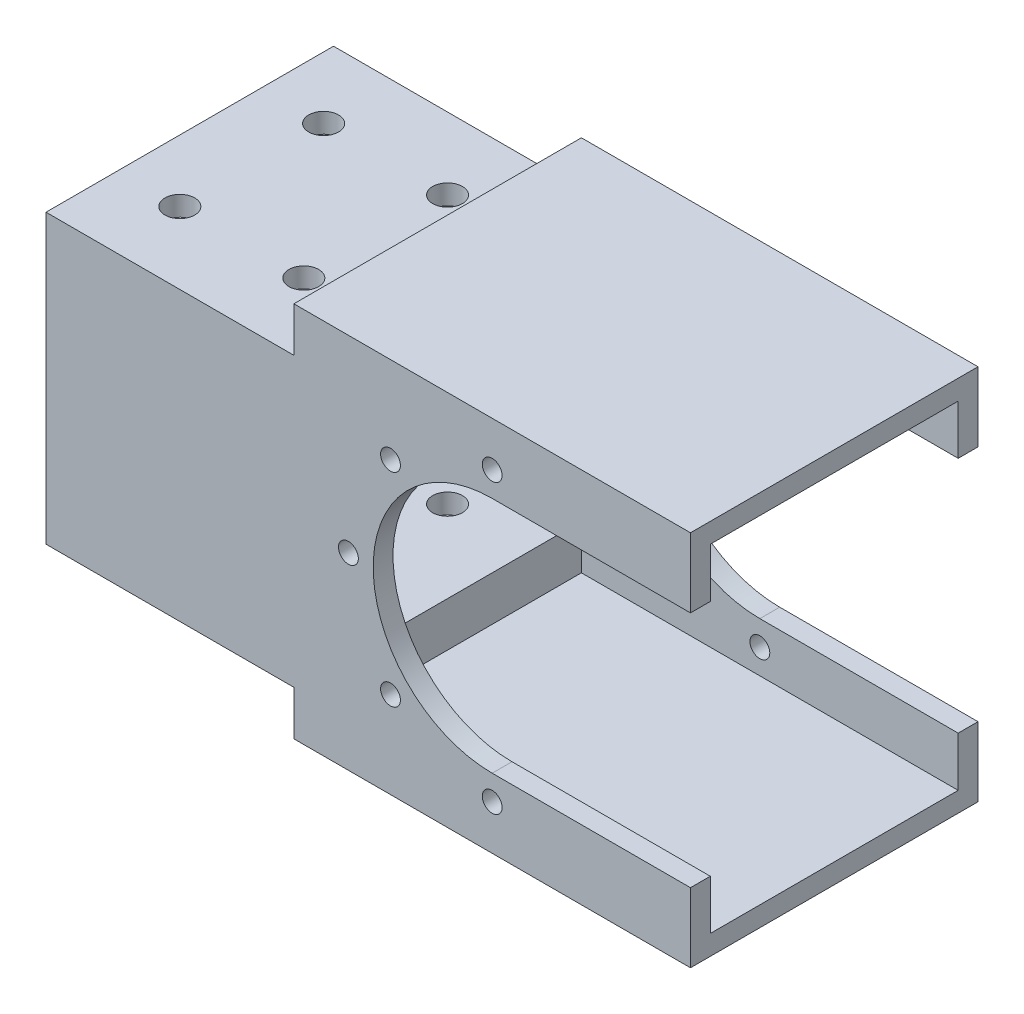
SolidWorks part; units mm, degrees
material "Plain Carbon Steel"
ref_plane "Front Plane" through (0, 0, 0) normal (0, 0, 1) x (1, 0, 0)
ref_plane "Top Plane" through (0, 0, 0) normal (0, 1, 0) x (1, 0, 0)
ref_plane "Right Plane" through (0, 0, 0) normal (1, 0, 0) x (0, 0, -1)
sketch "Sketch1" plane through (0, 0, 0) normal (0, 0, 1) x (1, 0, 0)
  line L0 (25, -62.3909) -> (25, -29) construction
  line L1 (-25, -29) -> (25, -29)
  line L2 (-25, -29) -> (-25, 29)
  line L3 (-25, 29) -> (25, 29)
  line L5 (0, 29) -> (0, -29) construction
  line L6 (-25, 0) -> (50, 0) construction
  line L7 (25, 38) -> (25, 29)
  line L8 (25, 38) -> (105, 38)
  line L9 (25, -38) -> (105, -38)
  line L10 (105, 38) -> (105, -38)
  line L11 (25, 29) -> (25, 60.3909) construction
  line L12 (25, -29) -> (25, -38)
  point P0 (0, 0)
  point P4 (105, 0)
  point P7 (50, 0)
  dimension "D1" = 50
  dimension "D2" = 58
  dimension "D3" = 76
  dimension "D4" = 80
extrude "Boss-Extrude1" add sketch "Sketch1" along normal blind 58
shell "Shell1" thickness 4
sketch "Sketch2" plane through (0, 0, 0) normal (0, 0, -1) x (-1, 0, 0)
  line L0 (0, 0) -> (-208.0046, 0) construction
  line L1 (-65, 24) -> (-105, 24)
  line L2 (-105, -38) -> (-105, 38) construction
  line L3 (-105, 24) -> (-105, -24)
  line L4 (-105, -24) -> (-65, -24)
  arc A0 (-65, -24) -> (-65, 24) centre (-65, 0) ccw
  circle A1 centre (-65, 0) radius 29 construction
  circle A2 centre (-36, 0) radius 2
  circle A3 centre (-44.4939, -20.5061) radius 2
  circle A4 centre (-65, -29) radius 2
  circle A8 centre (-65, 29) radius 2
  circle A9 centre (-44.4939, 20.5061) radius 2
  arc A10 (-84.044, 21.8707) -> (-86.8707, 19.044) centre (-85.5061, 20.5061) ccw [skipped]
  arc A11 (-93.931, 1.9988) -> (-96, 0) centre (-94, 0) ccw [skipped]
  arc A12 (-86.8707, -19.044) -> (-84.044, -21.8707) centre (-85.5061, -20.5061) ccw [skipped]
  point P29 (-65, 0)
  dimension "D1" = 48
  dimension "D3" = 58
  dimension "D4" = 4
  dimension "D2" = 40
  dimension "D5" = 8
extrude "Cut-Extrude1" cut sketch "Sketch2" against normal blind 60
sketch "Sketch3" plane through (0, -29, 0) normal (0, -1, 0) x (1, 0, 0)
  line L0 (0, 0) -> (0, 58) construction
  line L1 (-25, 58) -> (25, 58) construction
  line L2 (-25, 29) -> (25, 29) construction
  line L3 (-25, 58) -> (-25, 0) construction
  line L4 (25, 58) -> (25, 0) construction
  circle A0 centre (12.5, 43.5) radius 3
  circle A1 centre (-12.5, 43.5) radius 3
  circle A2 centre (-12.5, 14.5) radius 3
  circle A3 centre (12.5, 14.5) radius 3
  dimension "D1" = 6
  dimension "D2" = 12.5
  dimension "D3" = 14.5
extrude "Cut-Extrude2" cut sketch "Sketch3" against normal blind 70
